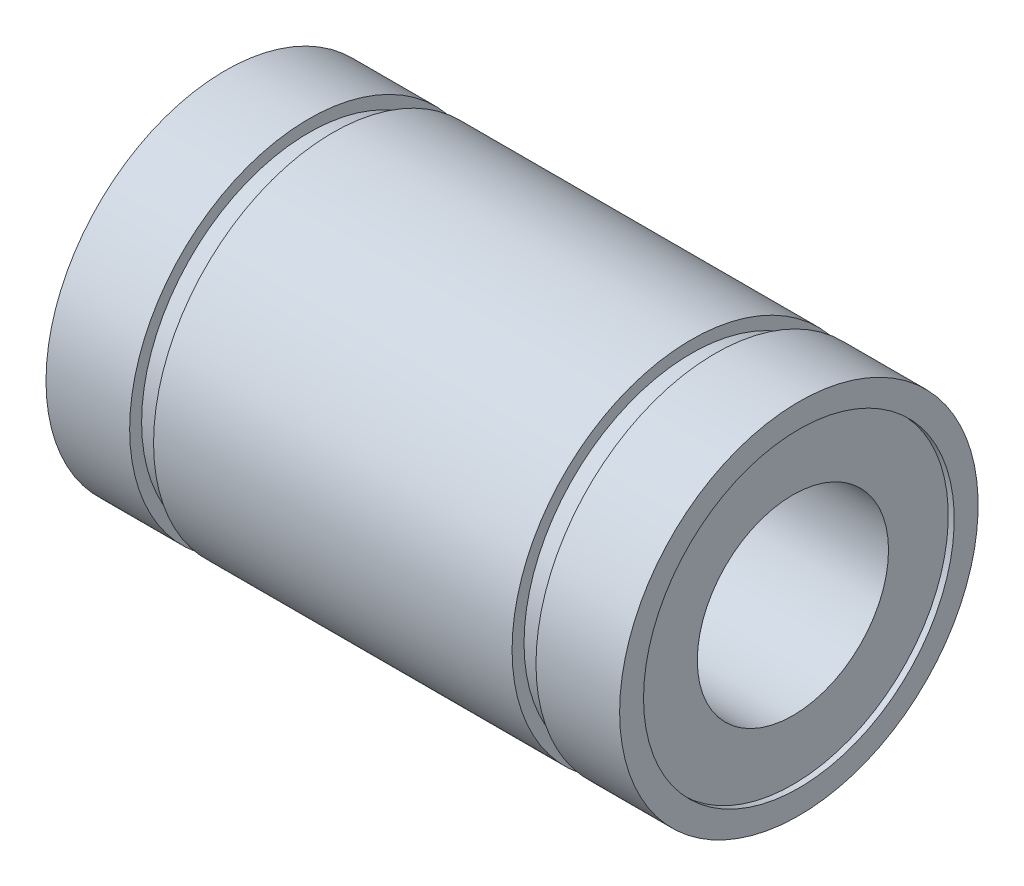
SolidWorks part; units mm, degrees
ref_plane "Front Plane" through (0, 0, 0) normal (0, 0, 1) x (1, 0, 0)
ref_plane "Top Plane" through (0, 0, 0) normal (0, 1, 0) x (1, 0, 0)
ref_plane "Right Plane" through (0, 0, 0) normal (1, 0, 0) x (0, 0, -1)
sketch "Sketch1" plane through (0, 0, 0) normal (0, 1, 0) x (1, 0, 0)
  line L0 (-10.6667, 0) -> (25.8133, 0) construction
  line L17 (-11.75, 4) -> (11.75, 4)
  line L18 (11.75, 4) -> (11.75, 6.5)
  line L19 (11.75, 6.5) -> (12, 6.5)
  line L20 (12, 6.5) -> (12, 7.5)
  line L21 (12, 7.5) -> (8.5, 7.5)
  line L22 (8.5, 7.5) -> (8.5, 7)
  line L23 (8.5, 7) -> (7.5, 7)
  line L24 (7.5, 7) -> (7.5, 7.5)
  line L25 (7.5, 7.5) -> (-7.5, 7.5)
  line L26 (-7.5, 7.5) -> (-7.5, 7)
  line L27 (-7.5, 7) -> (-8.5, 7)
  line L28 (-8.5, 7) -> (-8.5, 7.5)
  line L29 (-8.5, 7.5) -> (-12, 7.5)
  line L30 (-12, 7.5) -> (-12, 6.5)
  line L31 (-12, 6.5) -> (-11.75, 6.5)
  line L32 (-11.75, 6.5) -> (-11.75, 4)
  point P21 (0, 4)
  point P22 (0, 7.5)
  dimension "D1" = 24
  dimension "D2" = 4
  dimension "D3" = 7.5
  dimension "D4" = 0.25
  dimension "D5" = 1
  dimension "D6" = 0.5
  dimension "D7" = 1
  dimension "D8" = 3.5
revolve "Revolve1" add sketch "Sketch1" angle 360 about L0
